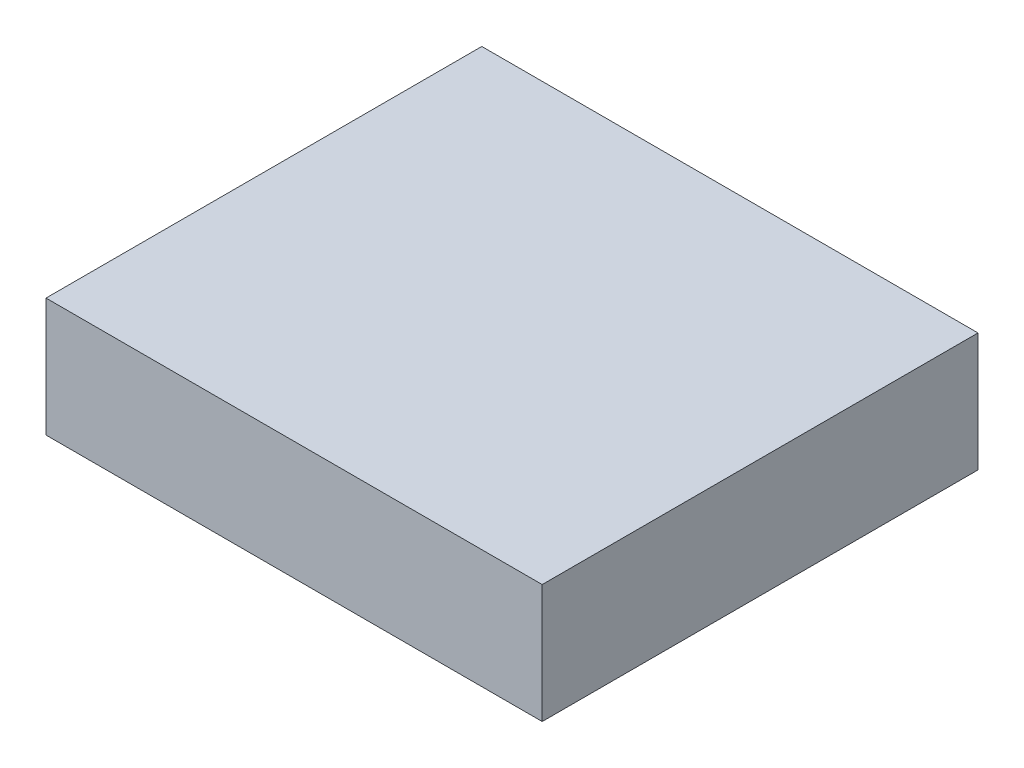
SolidWorks part; units mm, degrees
ref_plane "Front Plane" through (0, 0, 0) normal (0, 0, 1) x (1, 0, 0)
ref_plane "Top Plane" through (0, 0, 0) normal (0, 1, 0) x (1, 0, 0)
ref_plane "Right Plane" through (0, 0, 0) normal (1, 0, 0) x (0, 0, -1)
sketch "Sketch1" plane through (0, 0, 0) normal (0, 1, 0) x (1, 0, 0)
  line L1 (-57.5, -50.5) -> (57.5, -50.5)
  line L2 (-57.5, -50.5) -> (-57.5, 50.5)
  line L3 (-57.5, 50.5) -> (57.5, 50.5)
  line L4 (57.5, -50.5) -> (57.5, 50.5)
  line L5 (-57.5, -50.5) -> (57.5, 50.5) construction
  line L6 (-57.5, 50.5) -> (57.5, -50.5) construction
  point P0 (0, 0)
  dimension "D1" = 101
  dimension "D2" = 115
extrude "Boss-Extrude1" add sketch "Sketch1" along normal blind 27.5
